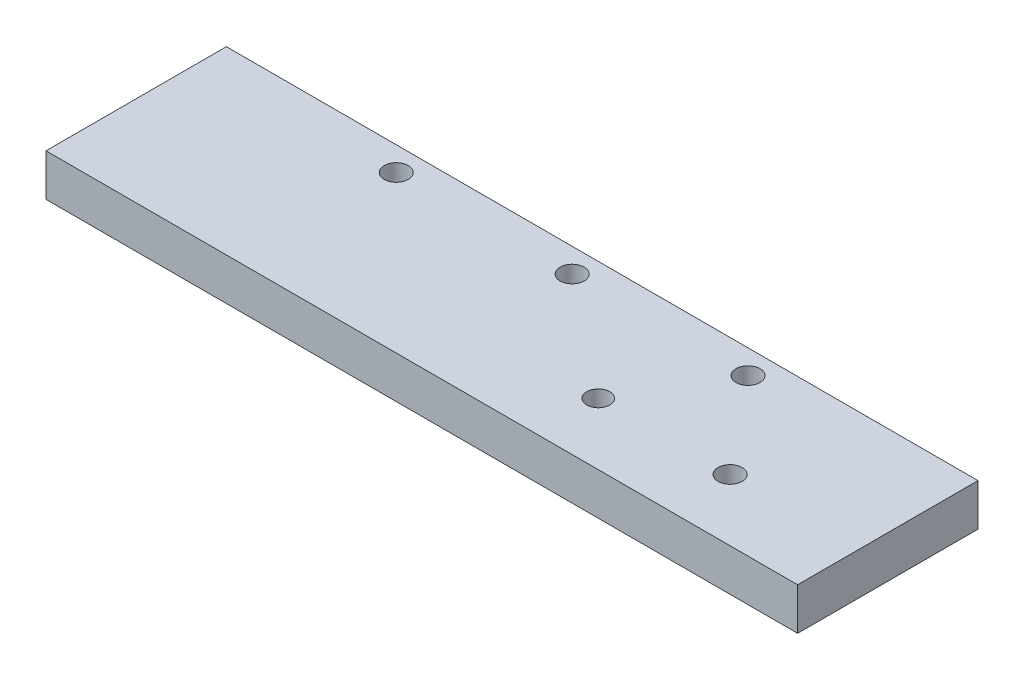
SolidWorks part; units mm, degrees
ref_plane "Front Plane" through (0, 0, 0) normal (0, 0, 1) x (1, 0, 0)
ref_plane "Top Plane" through (0, 0, 0) normal (0, 1, 0) x (1, 0, 0)
ref_plane "Right Plane" through (0, 0, 0) normal (1, 0, 0) x (0, 0, -1)
sketch "Sketch1" plane through (0, 0, 0) normal (0, 1, 0) x (1, 0, 0)
  line L1 (-102.5105, 65.1674) -> (22.4895, 65.1674)
  line L2 (-102.5105, 65.1674) -> (-102.5105, 35.1674)
  line L3 (-102.5105, 35.1674) -> (22.4895, 35.1674)
  line L4 (22.4895, 65.1674) -> (22.4895, 35.1674)
  dimension "D1" = 30
  dimension "D2" = 125
extrude "Boss-Extrude1" add sketch "Sketch1" along normal blind 7 contours L2 L3 L4 L1
sketch "Sketch2" plane through (0, 0, 0) normal (0, -1, 0) x (1, 0, 0)
  line L0 (-102.5105, -65.1674) -> (-102.5105, -35.1674) construction
  line L1 (-102.5105, -65.1674) -> (22.4895, -65.1674) construction
  circle A0 centre (-70.2605, -61.1674) radius 2
  circle A1 centre (-41.0105, -61.1674) radius 2
  circle A2 centre (-11.7605, -61.1674) radius 2
  circle A7 centre (-20.9297, -45.4354) radius 1.919
  circle A8 centre (0.9887, -45.4354) radius 2.0055
  dimension "D1" = 32.25
  dimension "D5" = 29.25
  dimension "D2" = 4
  dimension "D3" = 29.25
  dimension "D4" = 4
  dimension "D6" = 4
extrude "Cut-Extrude1" cut sketch "Sketch2" against normal blind 10
